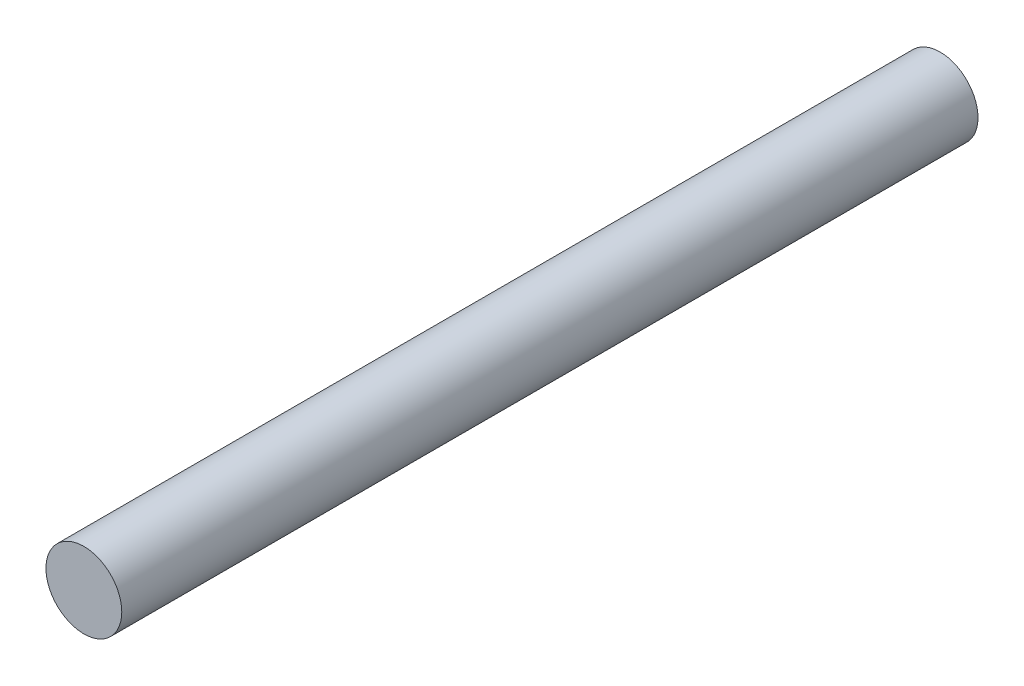
SolidWorks part; units mm, degrees
ref_plane "Front Plane" through (0, 0, 0) normal (0, 0, 1) x (1, 0, 0)
ref_plane "Top Plane" through (0, 0, 0) normal (0, 1, 0) x (1, 0, 0)
ref_plane "Right Plane" through (0, 0, 0) normal (1, 0, 0) x (0, 0, -1)
sketch "Sketch1" plane through (0, 0, 0) normal (0, 0, 1) x (1, 0, 0)
  circle A0 centre (-11.0125, 8.0178) radius 10
extrude "Boss-Extrude1" add sketch "Sketch1" along normal mid plane 225.8005
